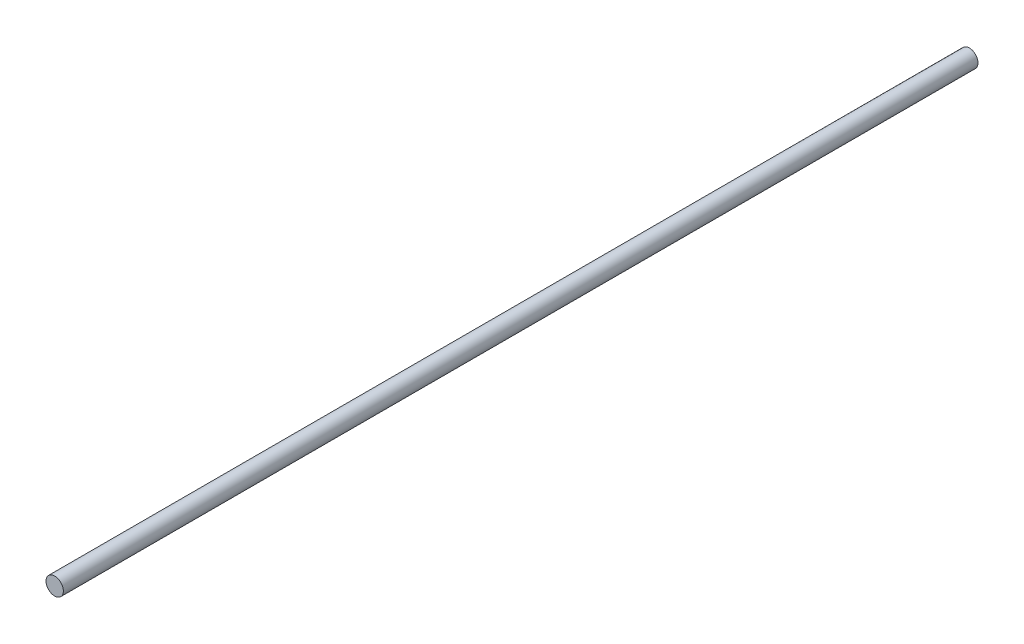
SolidWorks part; units mm, degrees
ref_plane "Front Plane" through (0, 0, 0) normal (0, 0, 1) x (1, 0, 0)
ref_plane "Top Plane" through (0, 0, 0) normal (0, 1, 0) x (1, 0, 0)
ref_plane "Right Plane" through (0, 0, 0) normal (1, 0, 0) x (0, 0, -1)
sketch "Sketch1" plane through (0, 0, 0) normal (0, 0, 1) x (1, 0, 0)
  circle A0 centre (0, 0) radius 2.375
  dimension "D1" = 4.75
extrude "Boss-Extrude1" add sketch "Sketch1" along normal blind 250
